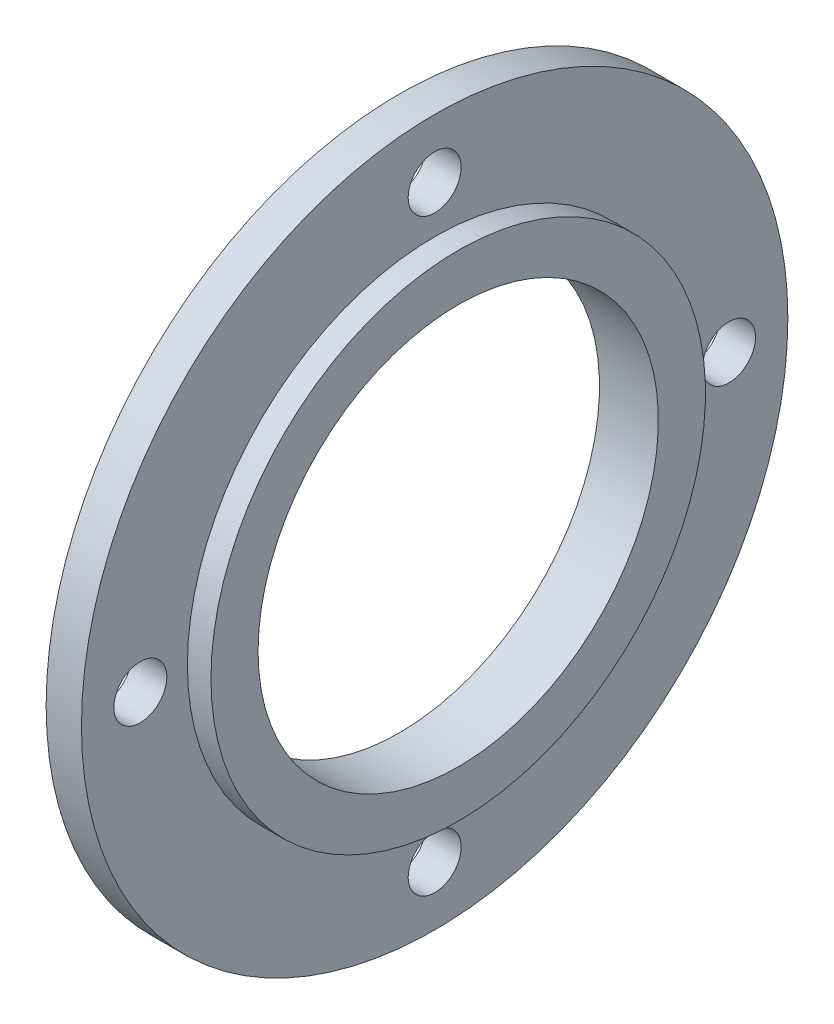
SolidWorks part; units mm, degrees
material "6061 Alloy"
ref_plane "Ön Düzlem" through (0, 0, 0) normal (0, 0, 1) x (1, 0, 0)
ref_plane "Üst Düzlem" through (0, 0, 0) normal (0, 1, 0) x (1, 0, 0)
ref_plane "Sağ Düzlem" through (0, 0, 0) normal (1, 0, 0) x (0, 0, -1)
sketch "Sketch1" plane through (0, 0, 0) normal (0, 0, 1) x (1, 0, 0)
  line L0 (0, 17) -> (5, 17)
  line L1 (5, 17) -> (5, 21)
  line L2 (5, 21) -> (3, 21)
  line L3 (3, 21) -> (3, 30)
  line L4 (3, 30) -> (0, 30)
  line L5 (0, 30) -> (0, 17)
  line L6 (0, 17) -> (0, 0) construction
  line L7 (0, 0) -> (7.3047, 0) construction
  dimension "D1" = 2
  dimension "D2" = 3
  dimension "D3" = 4
  dimension "D4" = 21
  dimension "D5" = 30
revolve "Revolve1" add sketch "Sketch1" angle 360 about L7
sketch "Sketch3" plane through (0, 0, 0) normal (-1, 0, 0) x (0, 0, 1)
  line L0 (0, 0) -> (0, 25) construction
  dimension "D1" = 25
hole_wizard "M4 Clearance Hole1" positions "Sketch4" profile "Sketch6" hole size "M4" standard "ISO" end condition up to next
sketch "Sketch4" plane through (0, 0, 0) normal (-1, 0, 0) x (0, 0, 1)
  point P0 (0, 25)
sketch "Sketch6" plane through (0, 25, 0) normal (0, 1, 0) x (0, 0, 1)
  line L0 (0, 0) -> (0, 3.001)
  line L1 (0, 3.001) -> (2.25, 3.001)
  line L2 (2.25, 3.001) -> (2.25, 0)
  line L5 (2.25, 0) -> (0, 0)
  line L11 (0, -6.35) -> (0, 107.95) construction
  dimension "Thru Hole Dia." = 4.5
  dimension "Thru Hole Depth" = 3.001
pattern_circular "CirPattern1" count 4 over 360 about axis through (0, 0, 0) along (1, 0, 0) of "M4 Clearance Hole1"
